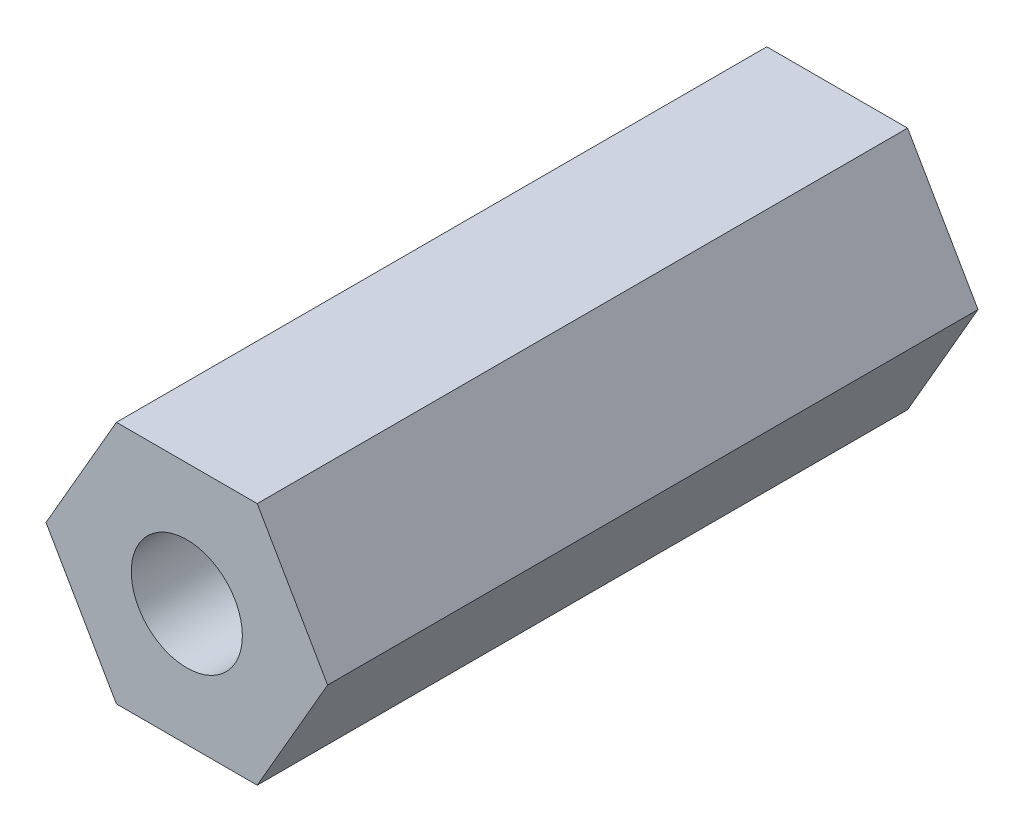
SolidWorks part; units mm, degrees
material "1060 合金"
ref_plane "前视基准面" through (0, 0, 0) normal (0, 0, 1) x (1, 0, 0)
ref_plane "上视基准面" through (0, 0, 0) normal (0, 1, 0) x (1, 0, 0)
ref_plane "右视基准面" through (0, 0, 0) normal (1, 0, 0) x (0, 0, -1)
other "Configuration Table"
sketch "草图1" plane through (0, 0, 0) normal (0, 0, 1) x (1, 0, 0)
  line L1 (-1.299, 2.25) -> (-2.5981, 0)
  line L2 (-2.5981, 0) -> (-1.299, -2.25)
  line L3 (-1.299, -2.25) -> (1.299, -2.25)
  line L4 (1.299, -2.25) -> (2.5981, 0)
  line L5 (2.5981, 0) -> (1.299, 2.25)
  line L6 (1.299, 2.25) -> (-1.299, 2.25)
  circle A0 centre (0, 0) radius 2.25 construction
  dimension "D1" = 4.5
extrude "凸台-拉伸1" add sketch "草图1" along normal blind 12
hole_wizard "M2.5 螺纹孔1" positions "草图2" profile "草图3" tap size "M2.5" standard "ISO"
sketch "草图2" plane through (0, 0, 12) normal (0, 0, 1) x (1, 0, 0)
  point P0 (0, 0)
sketch "草图3" plane through (0, 0, 12) normal (1, 0, 0) x (0, -1, 0)
  line L0 (0, 0) -> (0, 21.9659)
  line L1 (0, 21.9659) -> (1.025, 21.35)
  line L2 (1.025, 21.35) -> (1.025, 0)
  line L5 (1.025, 0) -> (0, 0)
  line L10 (0, 21.9659) -> (-1.025, 21.35) construction
  line L11 (0, -6.35) -> (0, 107.95) construction
  dimension "螺纹孔钻头直径" = 2.05
  dimension "螺纹孔钻头深度" = 21.35
  dimension "导头角度" = 118
cosmetic thread "孔螺蚊线1" parameters "D1"=20, "D2"=2.5
